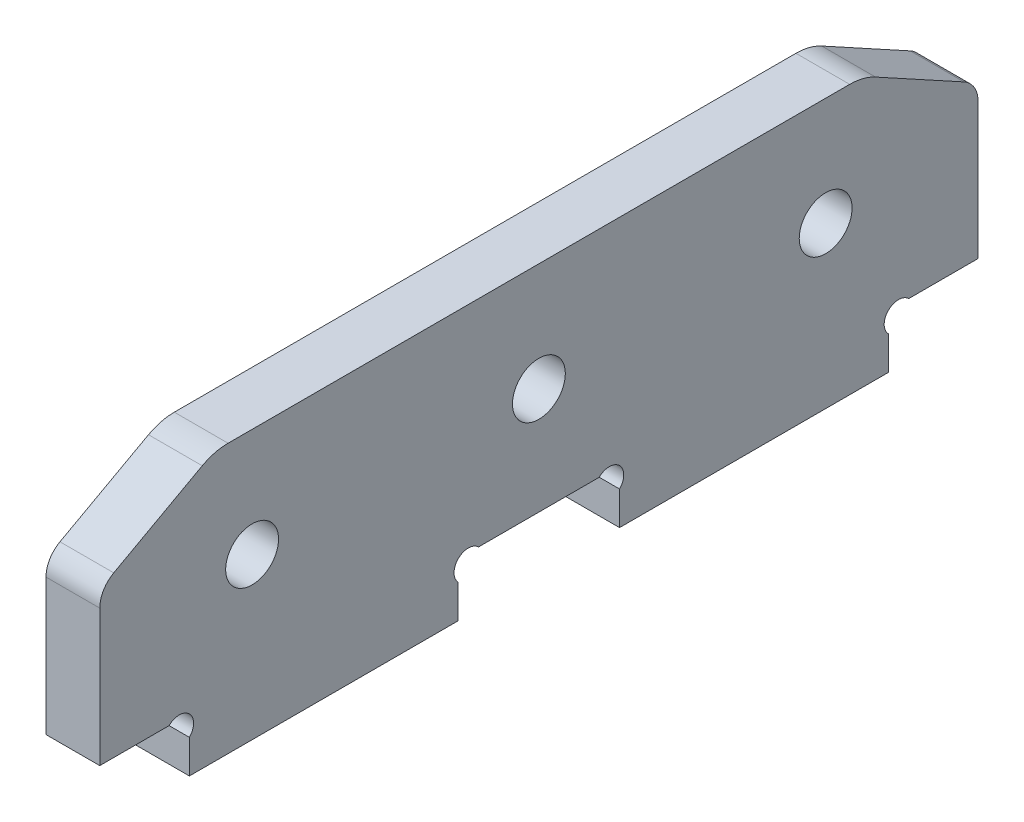
SolidWorks part; units mm, degrees
ref_plane "Plan de face" through (0, 0, 0) normal (0, 0, 1) x (1, 0, 0)
ref_plane "Plan de dessus" through (0, 0, 0) normal (0, 1, 0) x (1, 0, 0)
ref_plane "Plan de droite" through (0, 0, 0) normal (1, 0, 0) x (0, 0, -1)
sketch "Esquisse2" plane through (0, 0, 0) normal (1, 0, 0) x (0, 0, -1)
  line L0 (-29.1501, 0) -> (150.2531, 0) construction
  line L1 (-29.1501, 46) -> (150.2531, 46) construction
  line L2 (0, -14.812) -> (0, 86.1102) construction
  line L3 (133.511, 49.5822) -> (133.511, -20.5961) construction
  line L4 (17, 48.0325) -> (17, 8.6264) construction
  line L5 (-29.1501, 23) -> (38.9807, 23) construction
  line L6 (-29.1501, 6) -> (150.2531, 6) construction
  line L7 (49, -33.2148) -> (49, 59.323) construction
  line L8 (10, 12.1685) -> (10, -8.1986) construction
  line L9 (40, -8.1986) -> (40, 12.1685) construction
  line L10 (25, -5.9848) -> (25, -26.352) construction
  line L11 (14.3179, 17.92) -> (88, 17.92) construction
  line L12 (1.5591, 23.8538) -> (11.436, 29.2626)
  line L13 (96.4409, 23.8538) -> (86.564, 29.2626)
  line L14 (0, 21.2225) -> (0, 6)
  line L16 (40, 6) -> (53.7908, -7.7908) construction
  line L17 (98, 21.2225) -> (98, 6)
  line L18 (0, 6) -> (7.7373, 6)
  line L19 (10, 3.7373) -> (10, 0)
  line L20 (10, 0) -> (40, 0)
  line L21 (40, 0) -> (40, 3.7373)
  line L22 (58, 0) -> (58, 3.7373)
  line L23 (88, 0) -> (58, 0)
  line L24 (88, 3.7373) -> (88, 0)
  line L25 (98, 6) -> (90.2627, 6)
  line L27 (42.2627, 6) -> (55.7373, 6)
  line L28 (3, 30) -> (101.1843, 30) construction
  line L29 (14.3179, 30) -> (83.6821, 30)
  arc A0 (42.2627, 6) -> (40, 3.7373) centre (41.1314, 4.8686) ccw
  arc A1 (7.7373, 6) -> (10, 3.7373) centre (8.8686, 4.8686) cw
  circle A2 centre (17, 17.92) radius 2.95
  arc A3 (55.7373, 6) -> (58, 3.7373) centre (56.8686, 4.8686) cw
  arc A4 (90.2627, 6) -> (88, 3.7373) centre (89.1314, 4.8686) ccw
  circle A5 centre (81, 17.92) radius 2.95
  circle A6 centre (49, 17.92) radius 2.95
  arc A7 (0, 21.2225) -> (1.5591, 23.8538) centre (3, 21.2225) cw
  arc A8 (96.4409, 23.8538) -> (98, 21.2225) centre (95, 21.2225) cw
  arc A11 (11.436, 29.2626) -> (14.3179, 30) centre (14.3179, 24) cw
  arc A12 (83.6821, 30) -> (86.564, 29.2626) centre (83.6821, 24) cw
  point P36 (0, 23)
  point P61 (98, 23)
  point P75 (12.7826, 30)
  point P78 (85.2174, 30)
  dimension "D9" = 3
  dimension "D12" = 6
  dimension "D1" = 17
  dimension "D2" = 49
  dimension "D3" = 6
  dimension "D4" = 17
  dimension "D5" = 10
  dimension "D6" = 30
  dimension "D7" = 15
  dimension "D8" = 11.92
  dimension "D10" = 45
extrude "Extrusion1" add sketch "Esquisse2" along normal blind 6
